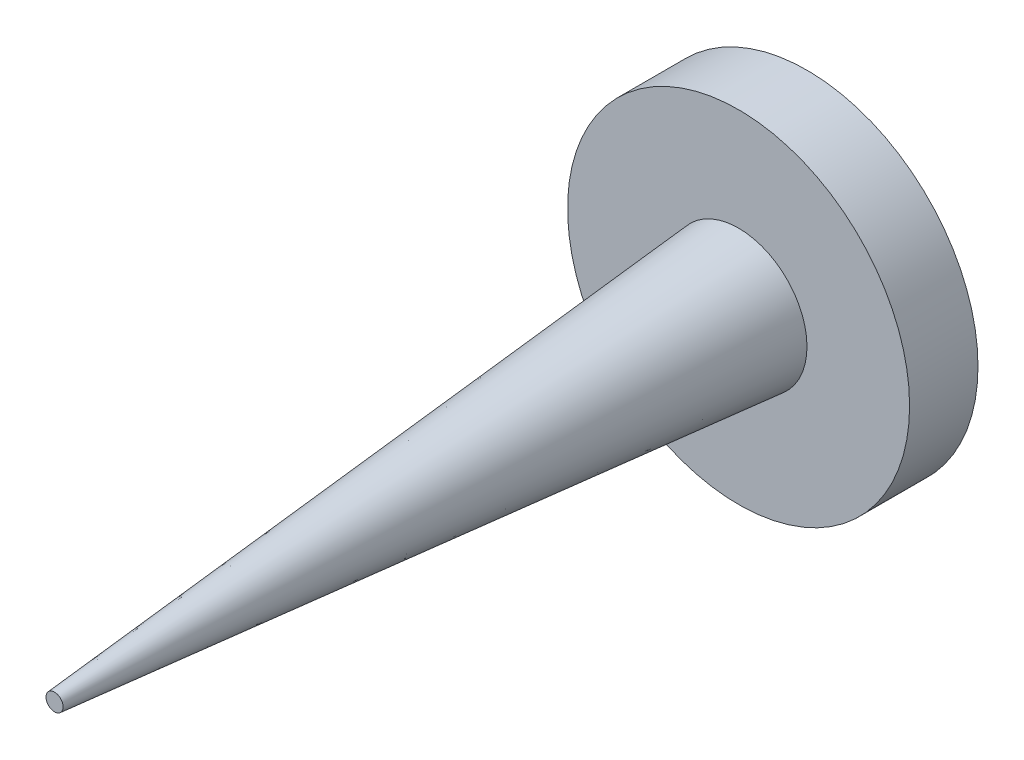
SolidWorks part; units mm, degrees
material "AISI 316 Stainless Steel Sheet (SS)"
ref_plane "Front Plane" through (0, 0, 0) normal (0, 0, 1) x (1, 0, 0)
ref_plane "Top Plane" through (0, 0, 0) normal (0, 1, 0) x (1, 0, 0)
ref_plane "Right Plane" through (0, 0, 0) normal (1, 0, 0) x (0, 0, -1)
sketch "Sketch1" plane through (0, 0, 0) normal (0, 0, 1) x (1, 0, 0)
  circle A0 centre (0, 0) radius 2.5
extrude "Boss-Extrude1" add sketch "Sketch1" along normal blind 1
sketch "Sketch2" plane through (0, 0, 1) normal (0, 0, 1) x (1, 0, 0)
  circle A0 centre (0, 0) radius 1
extrude "Boss-Extrude2" add sketch "Sketch2" along normal blind 10 draft 5
